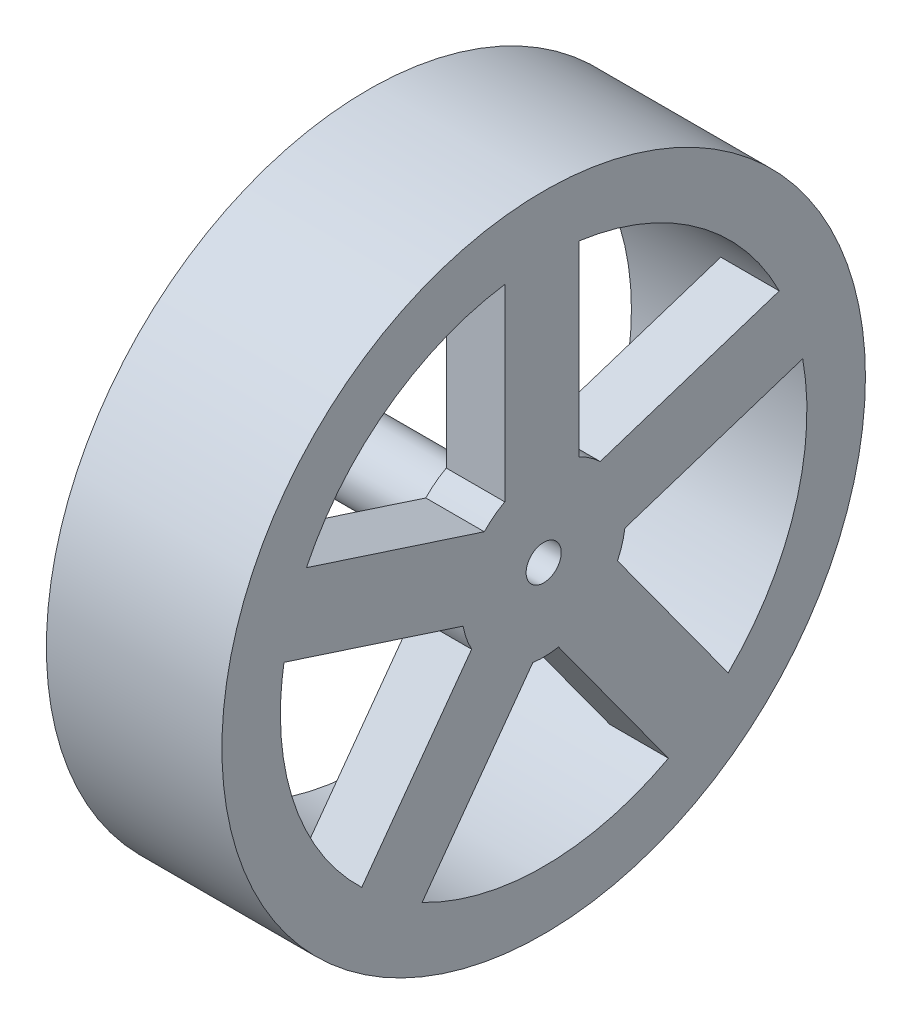
SolidWorks part; units mm, degrees
ref_plane "Front Plane" through (0, 0, 0) normal (0, 0, 1) x (1, 0, 0)
ref_plane "Top Plane" through (0, 0, 0) normal (0, 1, 0) x (1, 0, 0)
ref_plane "Right Plane" through (0, 0, 0) normal (1, 0, 0) x (0, 0, -1)
sketch "Sketch1" plane through (0, 0, 0) normal (1, 0, 0) x (0, 0, -1)
  circle A0 centre (0, 0) radius 27.5
  dimension "D1" = 55
extrude "Boss-Extrude1" add sketch "Sketch1" along normal blind 15
sketch "Sketch2" plane through (15, 0, 0) normal (1, 0, 0) x (0, 0, -1)
  circle A0 centre (0, 0) radius 1.5
  dimension "D1" = 3
extrude "Cut-Extrude1" cut sketch "Sketch2" against normal through all
sketch "Sketch3" plane through (0, 0, 0) normal (-1, 0, 0) x (0, 0, 1)
  circle A0 centre (0, 0) radius 22.5
  circle A1 centre (0, 0) radius 3
  dimension "D1" = 45
  dimension "D2" = 6
extrude "Cut-Extrude2" cut sketch "Sketch3" against normal blind 10
sketch "Sketch4" plane through (0, 0, 0) normal (-1, 0, 0) x (0, 0, 1)
  circle A0 centre (0, 0) radius 3
  circle A1 centre (0, 0) radius 1.5
extrude "Boss-Extrude2" add sketch "Sketch4" along normal blind 3
sketch "Sketch5" plane through (10, 0, 0) normal (-1, 0, 0) x (0, 0, 1)
  line L0 (27.9322, 12.2491) -> (5.0742, 4.822)
  line L1 (6.8859, -1.2588) -> (22.1913, 3.7142)
  line L2 (-3.018, 30.3503) -> (-3.018, 6.316)
  line L3 (20.2811, -22.78) -> (6.1541, -3.3358)
  line L4 (3.325, 6.1599) -> (3.325, 22.253)
  line L5 (0.9307, -6.9379) -> (10.3899, -19.9574)
  line L6 (-15.3978, -26.3279) -> (-1.2708, -6.8837)
  line L7 (-6.3107, -3.029) -> (-15.77, -16.0486)
  line L8 (-29.7975, 6.5085) -> (-6.9395, -0.9186)
  line L9 (-4.8309, 5.0658) -> (-20.1363, 10.0388)
  circle A0 centre (0, 0) radius 7
  circle A3 centre (0, 0) radius 22.5 construction
  point P29 (0, 0)
  circle M2 centre (0, 0) radius 22.5
  dimension "D1" = 14
  dimension "D2" = 5
extrude "Cut-Extrude3" cut sketch "Sketch5" against normal through all contours A0 L0 L4 M2 | A0 L2 L9 M2 | A0 L8 L7 M2 | A0 L6 L5 M2 | A0 L3 L1 M2
